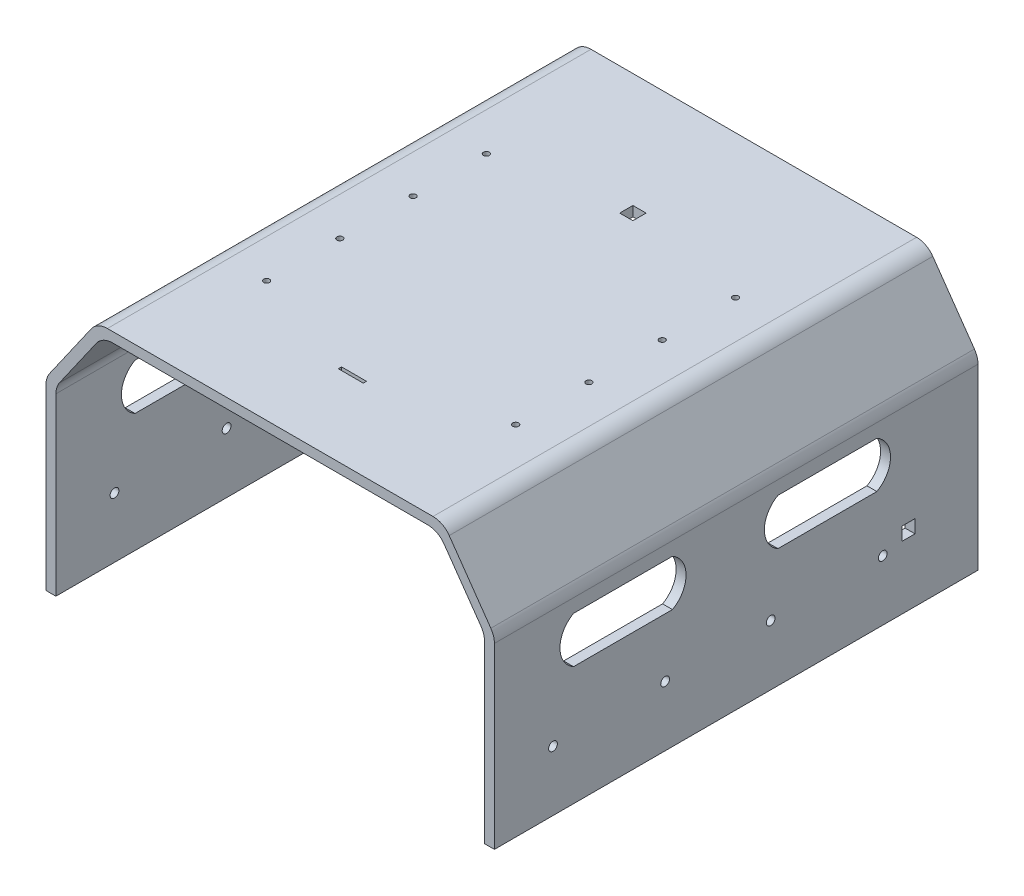
SolidWorks part; units mm, degrees
material "ABS"
ref_plane "Alzado" through (0, 0, 0) normal (0, 0, 1) x (1, 0, 0)
ref_plane "Planta" through (0, 0, 0) normal (0, 1, 0) x (1, 0, 0)
ref_plane "Vista lateral" through (0, 0, 0) normal (1, 0, 0) x (0, 0, -1)
sketch "Croquis1" plane through (0, 0, 0) normal (0, 0, 1) x (1, 0, 0)
  line L6 (0, 0) -> (0, 280)
  line L13 (0, -55) -> (0, 55) construction
  line L15 (0, 280) -> (77.5, 390.6815)
  line L17 (77.5, 390.6815) -> (602.5, 390.6815)
  line L18 (602.5, 390.6815) -> (680, 280)
  line L19 (680, 280) -> (680, 0)
  line L20 (15, 0) -> (15, 275.2705)
  line L21 (15, 275.2705) -> (85.3085, 375.6815)
  line L22 (85.3085, 375.6815) -> (594.6915, 375.6815)
  line L23 (594.6915, 375.6815) -> (665, 275.2705)
  line L24 (665, 275.2705) -> (665, 0)
  line L25 (15, 0) -> (0, 0)
  line L26 (665, 0) -> (680, 0)
  point P7 (650, 0)
  point P13 (665, 284.8076)
  point P14 (665, -15)
  point P15 (-15, -15)
  point P16 (-15, 284.0192)
  dimension "D1" = 280
  dimension "D2" = 680
  dimension "D3" = 125
  dimension "D4" = 125
  dimension "D6" = 15
  dimension "D5" = 525
extrude "Saliente-Extruir1" add sketch "Croquis1" along normal blind 700
fillet "Redondeo1" radius 30 8 edges at (665, 275.2705, 350) (594.6915, 375.6815, 350) (85.3085, 375.6815, 350) (15, 275.2705, 350) (680, 280, 350) (602.5, 390.6815, 350) (77.5, 390.6815, 350) (0, 280, 350)
sketch "Croquis16" plane through (680, 0, 0) normal (1, 0, 0) x (0, 0, -1)
  line L0 (-430, 180) -> (-580, 180)
  line L1 (-430, 250) -> (-580, 250)
  line L2 (-430, 180) -> (-580, 250) construction
  line L3 (-430, 250) -> (-580, 180) construction
  line L4 (-700, 0) -> (-700, 270.541) construction
  line L5 (-700, 0) -> (0, 0) construction
  arc A0 (-580, 250) -> (-580, 180) centre (-560.6351, 215) ccw
  arc A1 (-430, 180) -> (-430, 250) centre (-449.3649, 215) ccw
  point P0 (-505, 215)
  dimension "D3" = 40
  dimension "D4" = 40
  dimension "D1" = 70
  dimension "D2" = 150
  dimension "D5" = 120
  dimension "D6" = 180
extrude "Cortar-Extruir7" cut sketch "Croquis16" against normal through all
ref_plane "Plano1" through (0, 0, 350) normal (0, 0, 1) x (1, 0, 0)
mirror "Simetría1" about plane through (0, 0, 350) normal (0, 0, 1) of "Cortar-Extruir7"
scale "Escala1" scale about centroid uniform scaling yes scale factor 0.6
scale "Escala2" scale about centroid uniform scaling yes scale factor 0.75
sketch "Croquis17" plane through (0, 319.8165, 0) normal (0, -1, 0) x (1, 0, 0)
  line L0 (451.0973, 507.5) -> (228.9027, 507.5) construction
  line L2 (228.9027, 192.5) -> (228.9027, 507.5) construction
  circle A0 centre (255.0027, 425) radius 2
  circle A1 centre (255.0027, 375) radius 2
  circle A2 centre (425.0027, 425) radius 2
  circle A3 centre (255.0027, 325) radius 2
  circle A4 centre (255.0027, 275) radius 2
  circle A5 centre (425.0027, 375) radius 2
  circle A6 centre (425.0027, 325) radius 2
  circle A7 centre (425.0027, 275) radius 2
  dimension "D1" = 4
  dimension "D4" = 4
  dimension "D5" = 4
  dimension "D8" = 4
  dimension "D9" = 4
  dimension "D10" = 4
  dimension "D11" = 4
  dimension "D12" = 4
  dimension "D2" = 50
  dimension "D3" = 170
  dimension "D6" = 50
  dimension "D7" = 50
  dimension "D13" = 82.5
  dimension "D14" = 26.1
extrude "Cortar-Extruir8" cut sketch "Croquis17" against normal blind 10
sketch "Croquis18" plane through (493, 0, 0) normal (1, 0, 0) x (0, 0, -1)
  line L0 (-453.5, 231.7598) -> (-386, 231.7598) construction
  line L1 (-507.5, 150.7598) -> (-507.5, 272.5033) construction
  circle A0 centre (-467.5, 191.7598) radius 3
  circle A1 centre (-391, 191.7598) radius 3
  circle A2 centre (-319, 191.7598) radius 3
  circle A3 centre (-242.5, 191.7598) radius 3
  dimension "D1" = 6
  dimension "D2" = 6
  dimension "D3" = 6
  dimension "D4" = 6
  dimension "D5" = 76.5
  dimension "D6" = 72
  dimension "D7" = 76.5
  dimension "D8" = 40
  dimension "D9" = 40
extrude "Cortar-Extruir9" cut sketch "Croquis18" against normal through all
sketch "Croquis19" plane through (0, 326.5665, 0) normal (0, 1, 0) x (1, 0, 0)
  line L0 (348.5, -452.5) -> (331.5, -452.5)
  line L1 (348.5, -452.5) -> (348.5, -450.3)
  line L2 (348.5, -450.3) -> (331.5, -450.3)
  line L3 (331.5, -452.5) -> (331.5, -450.3)
  line L4 (451.0973, -507.5) -> (228.9027, -507.5) construction
  point P4 (340, -452.5)
  point P7 (340, -507.5)
  dimension "D1" = 17
  dimension "D2" = 2.2
  dimension "D3" = 55
extrude "Cortar-Extruir10" cut sketch "Croquis19" against normal through all
sketch "Croquis21" plane through (486.25, 0, 0) normal (-1, 0, 0) x (0, 0, 1)
  line L0 (507.5, 150.7598) -> (192.5, 150.7598) construction
  line L1 (220.5, 193.7598) -> (229.5, 193.7598)
  line L2 (220.5, 193.7598) -> (220.5, 202.7598)
  line L3 (220.5, 202.7598) -> (229.5, 202.7598)
  line L4 (229.5, 193.7598) -> (229.5, 202.7598)
  line L5 (192.5, 272.5033) -> (192.5, 150.7598) construction
  point P6 (220.5, 198.2598)
  dimension "D1" = 43
  dimension "D2" = 9
  dimension "D3" = 9
  dimension "D4" = 28
extrude "Cortar-Extruir11" cut sketch "Croquis21" against normal through all both and the other way through all
sketch "Croquis22" plane through (0, 319.8165, 0) normal (0, -1, 0) x (1, 0, 0)
  line L0 (232.4165, 192.5) -> (447.5835, 192.5) construction
  line L1 (335.5, 255.5) -> (344.5, 255.5)
  line L2 (335.5, 255.5) -> (335.5, 264.5)
  line L3 (335.5, 264.5) -> (344.5, 264.5)
  line L4 (344.5, 255.5) -> (344.5, 264.5)
  point P6 (340, 255.5)
  point P7 (340, 192.5)
  dimension "D1" = 63
  dimension "D2" = 9
extrude "Cortar-Extruir12" cut sketch "Croquis22" against normal through all
sketch "Croquis24" plane through (0, 0, 192.5) normal (0, 0, -1) x (-1, 0, 0)
  line L0 (-187, 272.5033) -> (-187, 150.7598) construction
  line L1 (-217.8441, 320.8098) -> (-189.4414, 280.2466) construction
  line L2 (-451.0973, 326.5665) -> (-228.9027, 326.5665) construction
  line L3 (-493, 150.7598) -> (-493, 272.5033) construction
  line L4 (-490.5586, 280.2466) -> (-462.1559, 320.8098) construction
  line L5 (-187, 272.5033) -> (-187, 150.7598)
  line L6 (-217.8441, 320.8098) -> (-189.4414, 280.2466)
  line L7 (-451.0973, 326.5665) -> (-228.9027, 326.5665)
  line L8 (-493, 150.7598) -> (-493, 272.5033)
  line L9 (-490.5586, 280.2466) -> (-462.1559, 320.8098)
  line L10 (-473, 150.7598) -> (-473, 270.4539)
  line L11 (-473, 270.4539) -> (-447.7137, 306.5665)
  line L12 (-447.7137, 306.5665) -> (-232.2863, 306.5665)
  line L13 (-232.2863, 306.5665) -> (-207, 270.4539)
  line L14 (-207, 270.4539) -> (-207, 150.7598)
  line L15 (-473, 150.7598) -> (-493, 150.7598)
  line L16 (-207, 150.7598) -> (-187, 150.7598)
  arc A0 (-187, 272.5033) -> (-189.4414, 280.2466) centre (-200.5, 272.5033) ccw construction
  arc A1 (-217.8441, 320.8098) -> (-228.9027, 326.5665) centre (-228.9027, 313.0665) ccw construction
  arc A2 (-451.0973, 326.5665) -> (-462.1559, 320.8098) centre (-451.0973, 313.0665) ccw construction
  arc A3 (-490.5586, 280.2466) -> (-493, 272.5033) centre (-479.5, 272.5033) ccw construction
  arc A4 (-187, 272.5033) -> (-189.4414, 280.2466) centre (-200.5, 272.5033) ccw
  arc A5 (-217.8441, 320.8098) -> (-228.9027, 326.5665) centre (-228.9027, 313.0665) ccw
  arc A6 (-451.0973, 326.5665) -> (-462.1559, 320.8098) centre (-451.0973, 313.0665) ccw
  arc A7 (-490.5586, 280.2466) -> (-493, 272.5033) centre (-479.5, 272.5033) ccw
  arc A8 (-473, 270.4539) -> (-473, 270.4539) centre (-473, 270.4539) ccw
  arc A9 (-447.7137, 306.5665) -> (-447.7137, 306.5665) centre (-447.7137, 306.5665) ccw
  arc A10 (-232.2863, 306.5665) -> (-232.2863, 306.5665) centre (-232.2863, 306.5665) ccw
  arc A11 (-207, 270.4539) -> (-207, 270.4539) centre (-207, 270.4539) ccw
  dimension "D1" = 20
extrude "Saliente-Extruir3" add sketch "Croquis24" along normal blind 15
sketch "Croquis26" plane through (0, 0, 177.5) normal (0, 0, -1) x (-1, 0, 0)
  line L0 (-385, 314.5665) -> (-295, 314.5665) construction
  line L1 (-228.9027, 326.5665) -> (-451.0973, 326.5665) construction
  line L2 (-447.7137, 306.5665) -> (-232.2863, 306.5665) construction
  line L3 (-493, 150.7598) -> (-473, 150.7598) construction
  line L4 (-473, 150.7598) -> (-473, 270.4539) construction
  line L5 (-207, 150.7598) -> (-187, 150.7598) construction
  line L6 (-207, 270.4539) -> (-207, 150.7598) construction
  line L7 (-493, 200.7598) -> (-187, 200.7598) construction
  line L8 (-493, 272.5033) -> (-493, 150.7598) construction
  line L9 (-187, 150.7598) -> (-187, 272.5033) construction
  circle A0 centre (-385, 314.5665) radius 2
  circle A1 centre (-295, 314.5665) radius 2
  circle A2 centre (-481, 160.7598) radius 2
  circle A3 centre (-199, 160.7598) radius 2
  circle A4 centre (-199, 240.7598) radius 2
  circle A5 centre (-481, 240.7598) radius 2
  point P4 (-340, 314.5665)
  point P7 (-340, 326.5665)
  dimension "D1" = 4
  dimension "D2" = 4
  dimension "D4" = 8
  dimension "D5" = 4
  dimension "D6" = 4
  dimension "D7" = 10
  dimension "D10" = 8
  dimension "D3" = 90
  dimension "D8" = 8
  dimension "D9" = 10
  dimension "D11" = 50
extrude "Cortar-Extruir13" cut sketch "Croquis26" against normal through all
